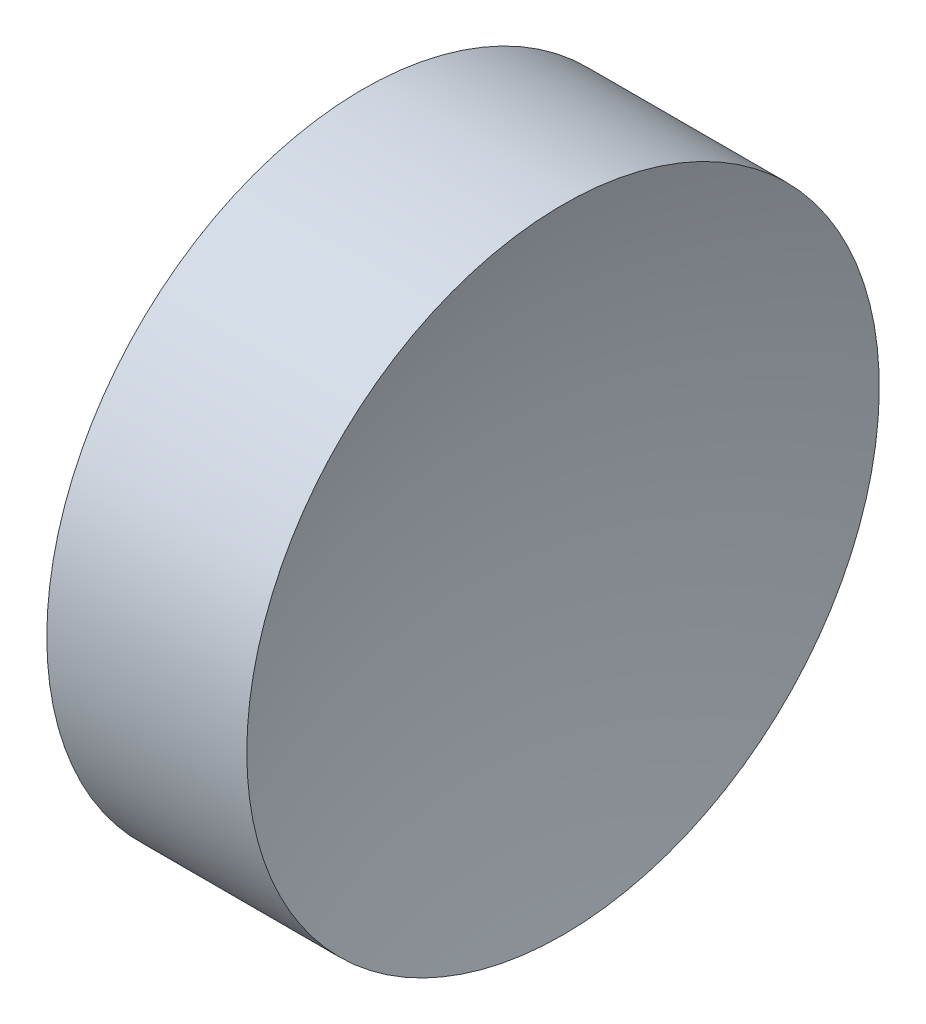
SolidWorks part; units mm, degrees
ref_plane "前视基准面" through (0, 0, 0) normal (0, 0, 1) x (1, 0, 0)
ref_plane "上视基准面" through (0, 0, 0) normal (0, 1, 0) x (1, 0, 0)
ref_plane "右视基准面" through (0, 0, 0) normal (1, 0, 0) x (0, 0, -1)
sketch "草图1" plane through (0, 0, 0) normal (0, 0, 1) x (1, 0, 0)
  line L0 (20.684, 13.0311) -> (26.997, 13.0311) construction
  line L1 (22.3093, 13.0311) -> (22.3093, 16.1811)
  line L2 (22.3093, 16.1811) -> (24.3013, 16.1811)
  line L3 (23.8093, 13.0311) -> (22.3093, 13.0311)
  arc A0 (24.3013, 16.1811) -> (23.8093, 13.0311) centre (34.1393, 13.0311) ccw
revolve "旋转1" add sketch "草图1" angle 360 about L0
